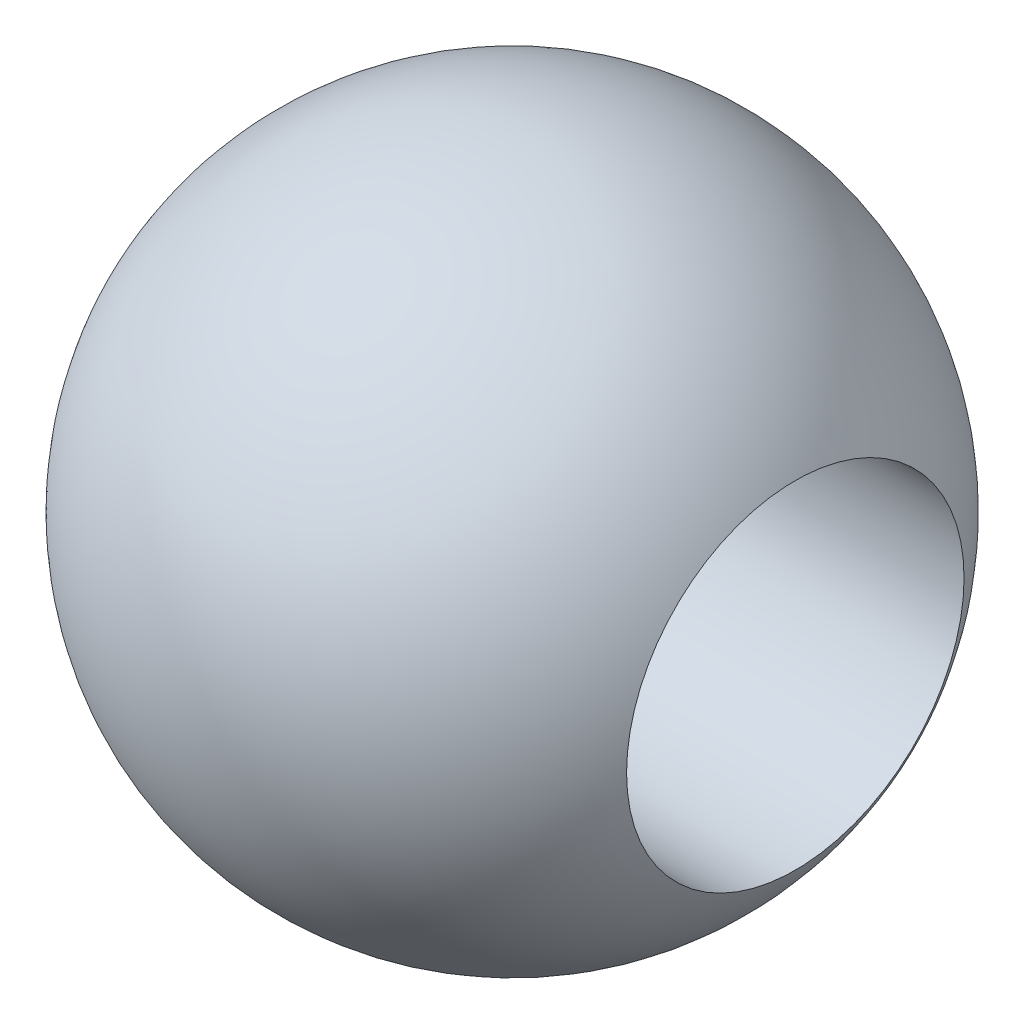
SolidWorks part; units mm, degrees
ref_plane "Front" through (0, 0, 0) normal (0, 0, 1) x (1, 0, 0)
ref_plane "Top" through (0, 0, 0) normal (0, 1, 0) x (1, 0, 0)
ref_plane "Right" through (0, 0, 0) normal (1, 0, 0) x (0, 0, -1)
sketch "Sketch1" plane through (0, 0, 0) normal (0, 0, 1) x (1, 0, 0)
  line L0 (0, 2.93) -> (0, -2.93)
  line L1 (0, 11.6413) -> (0, -7.1077) construction
  arc A0 (0, -2.93) -> (0, 2.93) centre (0, 0) ccw
  dimension "D1" = 5.86
revolve "Revolve1" add sketch "Sketch1" angle 360 about L1
sketch "Sketch2" plane through (0, 0, 0) normal (1, 0, 0) x (0, 0, -1)
  circle A0 centre (0, 0) radius 1.5
  dimension "D1" = 3
extrude "Cut-Extrude1" cut sketch "Sketch2" against normal through all both and the other way through all
